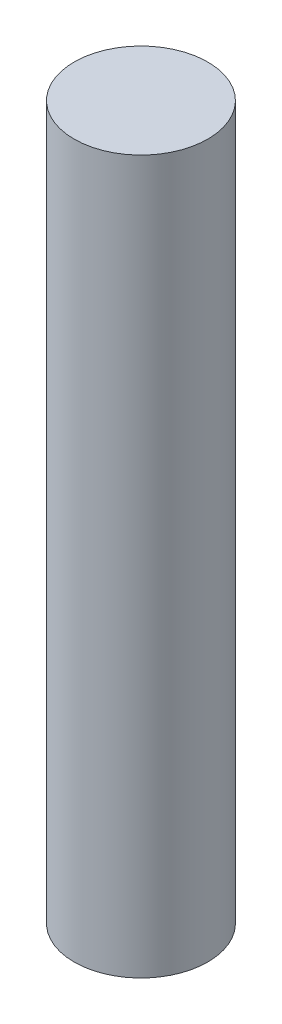
SolidWorks part; units mm, degrees
ref_plane "Front Plane" through (0, 0, 0) normal (0, 0, 1) x (1, 0, 0)
ref_plane "Top Plane" through (0, 0, 0) normal (0, 1, 0) x (1, 0, 0)
ref_plane "Right Plane" through (0, 0, 0) normal (1, 0, 0) x (0, 0, -1)
sketch "Sketch1" plane through (0, 0, 0) normal (0, 1, 0) x (1, 0, 0)
  circle A0 centre (0, 0) radius 2.3813
  dimension "D1" = 4.7625
extrude "Boss-Extrude1" add sketch "Sketch1" along normal blind 25.4
